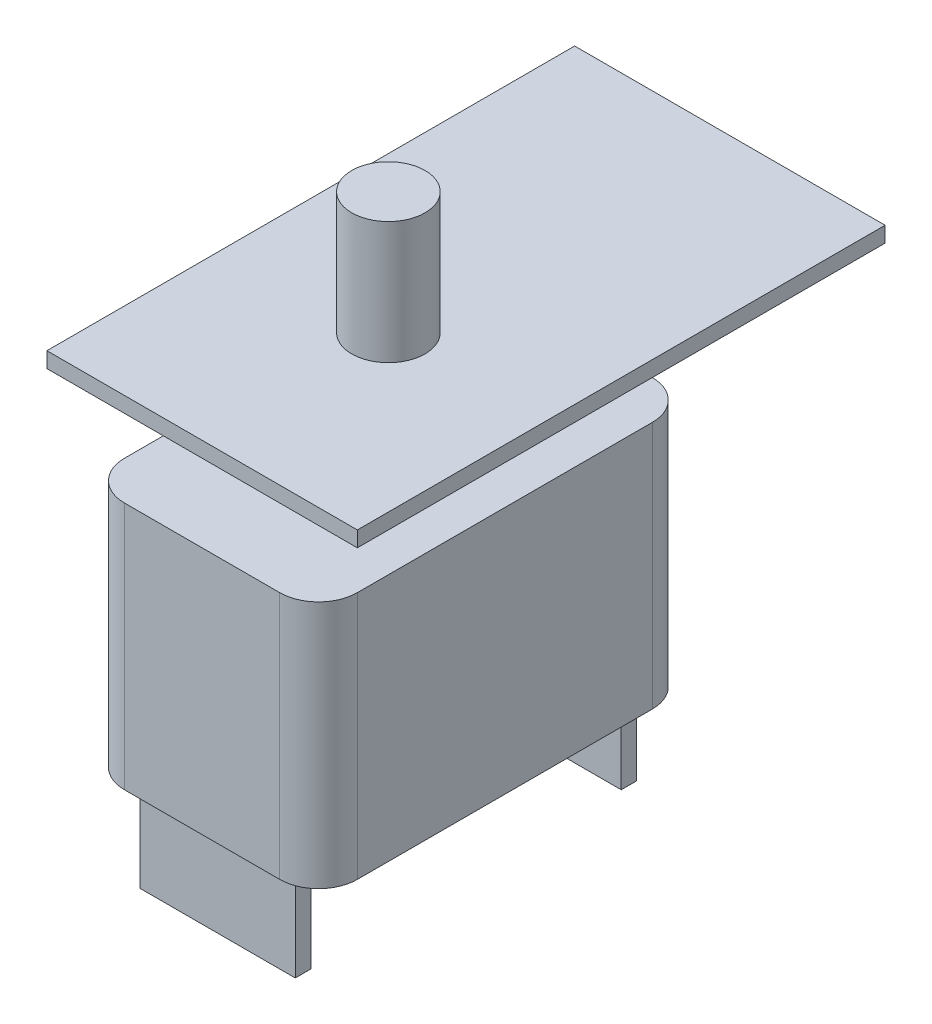
SolidWorks part; units mm, degrees
ref_plane "Front Plane" through (0, 0, 0) normal (0, 0, 1) x (1, 0, 0)
ref_plane "Top Plane" through (0, 0, 0) normal (0, 1, 0) x (1, 0, 0)
ref_plane "Right Plane" through (0, 0, 0) normal (1, 0, 0) x (0, 0, -1)
sketch "Sketch1" plane through (0, 0, 0) normal (0, 1, 0) x (1, 0, 0)
  line L1 (-9.525, 15.24) -> (9.525, 15.24)
  line L2 (-9.525, 15.24) -> (-9.525, -15.24)
  line L3 (-9.525, -15.24) -> (9.525, -15.24)
  line L4 (9.525, 15.24) -> (9.525, -15.24)
  line L5 (-9.525, 15.24) -> (9.525, -15.24) construction
  line L6 (-9.525, -15.24) -> (9.525, 15.24) construction
  point P0 (0, 0)
  dimension "D1" = 30.48
  dimension "D2" = 19.05
extrude "Boss-Extrude1" add sketch "Sketch1" along normal blind 20.32
fillet "Fillet1" radius 3.175 4 edges at (-9.525, 10.16, -15.24) (9.525, 10.16, -15.24) (-9.525, 10.16, 15.24) (9.525, 10.16, 15.24)
sketch "Sketch2" plane through (0, 20.32, 0) normal (0, 1, 0) x (1, 0, 0)
  circle A0 centre (0, 0) radius 6
  dimension "D1" = 12
extrude "Boss-Extrude2" add sketch "Sketch2" along normal blind 6.35
sketch "Sketch3" plane through (0, 0, 0) normal (0, -1, 0) x (1, 0, 0)
  line L0 (0, 15.24) -> (0, -15.24) construction
  line L1 (-6.35, 15.24) -> (6.35, 15.24) construction
  line L2 (6.35, -15.24) -> (-6.35, -15.24) construction
  line L3 (-9.525, 0) -> (9.525, 0) construction
  line L4 (-6.35, 13.97) -> (6.35, 13.97)
  line L5 (-6.35, 13.97) -> (-6.35, 12.7)
  line L6 (-6.35, 12.7) -> (6.35, 12.7)
  line L7 (6.35, 13.97) -> (6.35, 12.7)
  line L8 (-6.35, 13.97) -> (6.35, 12.7) construction
  line L9 (-6.35, 12.7) -> (6.35, 13.97) construction
  line L10 (-9.525, -12.065) -> (-9.525, 12.065) construction
  line L11 (9.525, 12.065) -> (9.525, -12.065) construction
  line L12 (-6.35, -12.7) -> (6.35, -13.97) construction
  line L13 (-6.35, -13.97) -> (6.35, -12.7) construction
  line L14 (6.35, -13.97) -> (6.35, -12.7)
  line L15 (-6.35, -12.7) -> (6.35, -12.7)
  line L16 (-6.35, -13.97) -> (-6.35, -12.7)
  line L17 (-6.35, -13.97) -> (6.35, -13.97)
  point P6 (0, 13.335)
  point P21 (0, -13.335)
  dimension "D1" = 12.7
  dimension "D2" = 1.27
  dimension "D3" = 1.27
extrude "Boss-Extrude3" add sketch "Sketch3" along normal blind 7.62
sketch "Sketch4" plane through (0, 26.67, 0) normal (0, 1, 0) x (1, 0, 0)
  line L0 (0, 0) -> (0, 25.4) construction
  line L1 (-6.35, -15.24) -> (6.35, -15.24) construction
  line L2 (12.7, 27.94) -> (-12.7, 27.94)
  line L3 (12.7, 27.94) -> (12.7, -15.24)
  line L4 (12.7, -15.24) -> (-12.7, -15.24)
  line L5 (-12.7, 27.94) -> (-12.7, -15.24)
  line L6 (12.7, 27.94) -> (-12.7, -15.24) construction
  line L7 (12.7, -15.24) -> (-12.7, 27.94) construction
  line L8 (6.35, 15.24) -> (-6.35, 15.24) construction
  point P4 (0, 6.35)
  dimension "D1" = 25.4
  dimension "D2" = 25.4
  dimension "D3" = 12.7
extrude "Boss-Extrude4" add sketch "Sketch4" along normal blind 1.27
sketch "Sketch5" plane through (0, 27.94, 0) normal (0, 1, 0) x (1, 0, 0)
  circle A0 centre (0, 0) radius 3
  dimension "D1" = 6
extrude "Boss-Extrude5" add sketch "Sketch5" along normal blind 10
